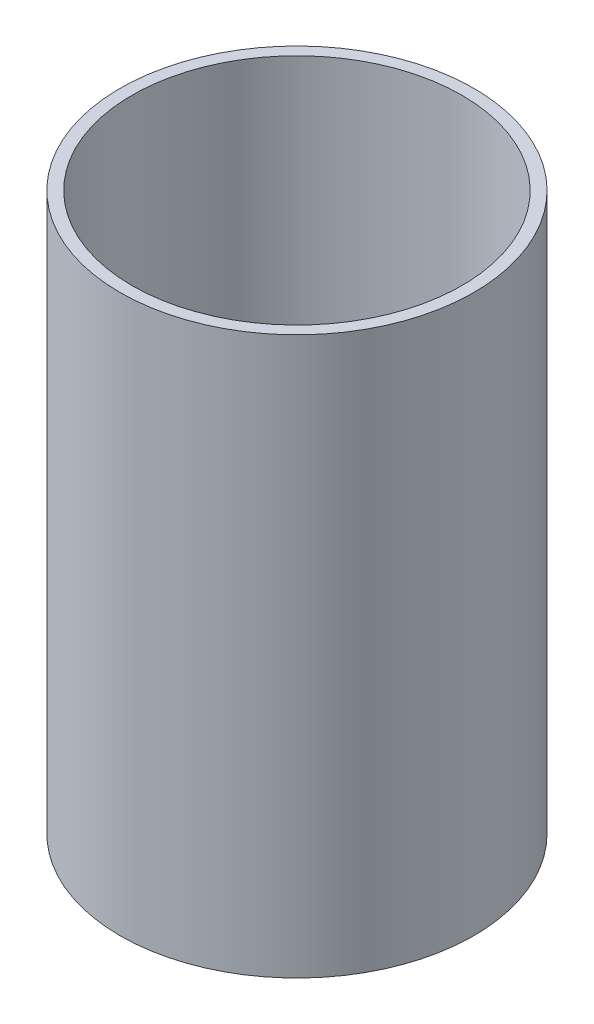
SolidWorks part; units mm, degrees
ref_plane "Plano frontal" through (0, 0, 0) normal (0, 0, 1) x (1, 0, 0)
ref_plane "Plano superior" through (0, 0, 0) normal (0, 1, 0) x (1, 0, 0)
ref_plane "Plano direito" through (0, 0, 0) normal (1, 0, 0) x (0, 0, -1)
sketch "Esboço1" plane through (0, 0, 0) normal (0, 1, 0) x (1, 0, 0)
  circle A0 centre (0, 0) radius 44.45
  circle A1 centre (0, 0) radius 41.45
extrude "Ressalto-extrusão1" add sketch "Esboço1" along normal blind 140
